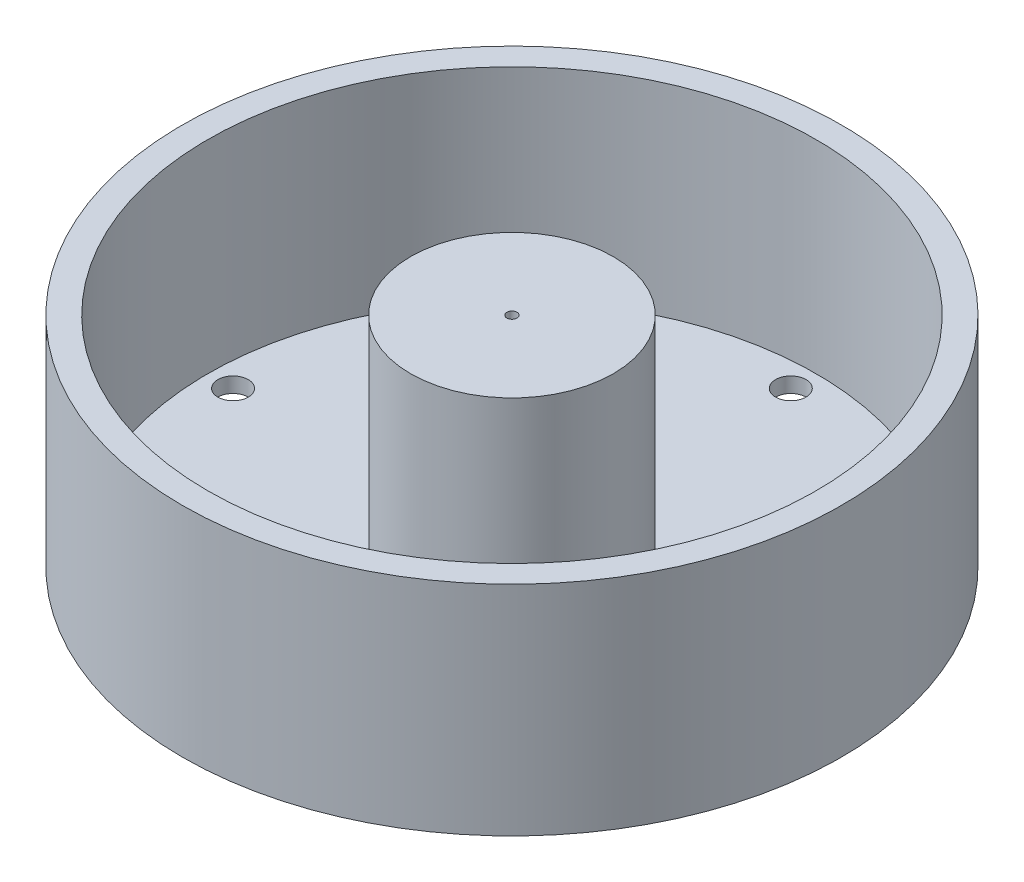
SolidWorks part; units mm, degrees
ref_plane "Front Plane" through (0, 0, 0) normal (0, 0, 1) x (1, 0, 0)
ref_plane "Top Plane" through (0, 0, 0) normal (0, 1, 0) x (1, 0, 0)
ref_plane "Right Plane" through (0, 0, 0) normal (1, 0, 0) x (0, 0, -1)
sketch "Sketch1" plane through (0, 0, 0) normal (0, 1, 0) x (1, 0, 0)
  circle A0 centre (0, 0) radius 65
  dimension "D1" = 130
extrude "Boss-Extrude1" add sketch "Sketch1" along normal blind 3
sketch "Sketch2" plane through (0, 3, 0) normal (0, 1, 0) x (1, 0, 0)
  circle A0 centre (0, 0) radius 55 construction
  circle A1 centre (0, 55) radius 3
  dimension "D1" = 110
  dimension "D2" = 6
extrude "Cut-Extrude1" cut sketch "Sketch2" against normal through all
pattern_circular "CirPattern1" count 4 over 360 about axis through (0, 0, 0) along (0, 1, 0) of "Cut-Extrude1"
sketch "Sketch3" plane through (0, 3, 0) normal (0, 1, 0) x (1, 0, 0)
  circle A0 centre (0, 0) radius 65 construction
  circle A1 centre (0, 0) radius 65
  circle A2 centre (0, 0) radius 60
  dimension "D1" = 5
extrude "Boss-Extrude2" add sketch "Sketch3" along normal blind 40
sketch "Sketch4" plane through (0, 3, 0) normal (0, 1, 0) x (1, 0, 0)
  circle A1 centre (0, 0) radius 20
  dimension "D2" = 40
extrude "Boss-Extrude3" add sketch "Sketch4" along normal blind 40
sketch "Sketch5" plane through (0, 0, 0) normal (0, -1, 0) x (1, 0, 0)
  circle A0 centre (0, 0) radius 10
  dimension "D1" = 20
extrude "Cut-Extrude2" cut sketch "Sketch5" against normal blind 30
sketch "Sketch6" plane through (0, 43, 0) normal (0, 1, 0) x (1, 0, 0)
  circle A0 centre (0, 0) radius 1
  dimension "D1" = 2
extrude "Cut-Extrude3" cut sketch "Sketch6" against normal through all
